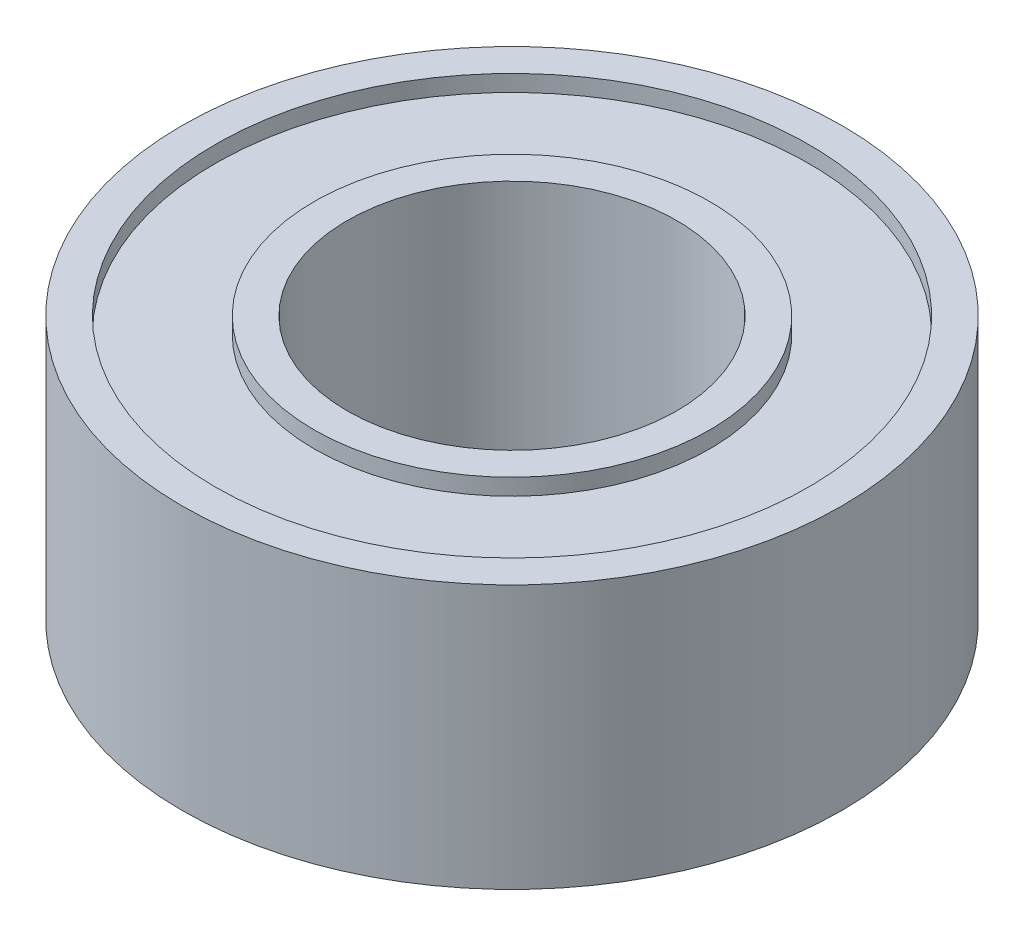
SolidWorks part; units mm, degrees
ref_plane "Front Plane" through (0, 0, 0) normal (0, 0, 1) x (1, 0, 0)
ref_plane "Top Plane" through (0, 0, 0) normal (0, 1, 0) x (1, 0, 0)
ref_plane "Right Plane" through (0, 0, 0) normal (1, 0, 0) x (0, 0, -1)
sketch "Sketch1" plane through (0, 0, 0) normal (0, 1, 0) x (1, 0, 0)
  circle A0 centre (0, 0) radius 5
  circle A1 centre (0, 0) radius 2.5
  dimension "D1" = 10
  dimension "D2" = 5
extrude "Boss-Extrude1" add sketch "Sketch1" along normal mid plane 4
sketch "Sketch2" plane through (0, 2, 0) normal (0, 1, 0) x (1, 0, 0)
  circle A2 centre (0, 0) radius 4.5
  circle A3 centre (0, 0) radius 4.5
  circle A5 centre (0, 0) radius 3
  circle A6 centre (0, 0) radius 3
  dimension "D1" = 0.5
  dimension "D2" = 0.5
extrude "Cut-Extrude1" cut sketch "Sketch2" against normal blind 0.25
mirror "Mirror1" about plane through (0, 0, 0) normal (0, 1, 0) of "Cut-Extrude1"
